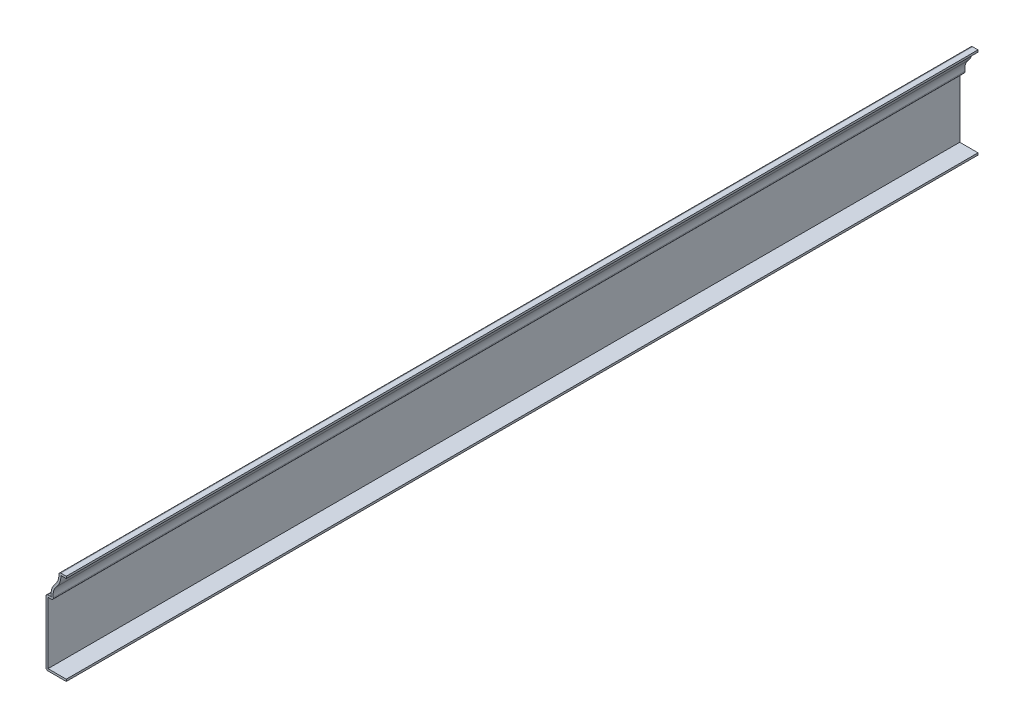
SolidWorks part; units mm, degrees
ref_plane "Front Plane" through (0, 0, 0) normal (0, 0, 1) x (1, 0, 0)
ref_plane "Top Plane" through (0, 0, 0) normal (0, 1, 0) x (1, 0, 0)
ref_plane "Right Plane" through (0, 0, 0) normal (1, 0, 0) x (0, 0, -1)
sketch "Sketch1" plane through (0, 0, 0) normal (0, 0, 1) x (1, 0, 0)
  line L0 (0, 0) -> (-12.7, 0)
  line L1 (-12.7, 0) -> (-12.7, 41.275)
  line L2 (-12.7, 41.275) -> (-9.3956, 41.275)
  line L3 (-4.7625, 57.15) -> (0, 57.15)
  line L4 (0, 57.15) -> (0, 0) construction
  arc A0 (-9.3956, 41.275) -> (-7.0791, 49.2125) centre (0, 42.8397) cw
  arc A1 (-7.0791, 49.2125) -> (-4.7625, 57.15) centre (-14.1581, 55.5853) ccw
  point P9 (-21.5439, 31.4867)
  point P11 (-9.4386, 31.3656)
  point P12 (-5.5649, 43.3499)
  point P13 (-5.7901, 49.6762)
  point P14 (-9.4617, 41.275)
  point P15 (-6.3623, 48.5795)
  point P16 (-9.3301, 41.275)
  point P17 (-9.3301, 41.275)
  point P18 (0, 0)
  point P19 (0, 0)
  dimension "D5" = 9.525
  dimension "D6" = 9.525
  dimension "D1" = 57.15
  dimension "D2" = 12.7
  dimension "D3" = 41.275
  dimension "D4" = 7.9375
extrude "Extrude-Thin1" add sketch "Sketch1" against normal blind 571.5 thin
fillet "Fillet1" radius 1.27 4 edges at (-12.7, 0, -285.75) (-7.753, 40.005, -285.75) (-12.7, 41.275, -285.75) (-4.7625, 57.15, -285.75)
